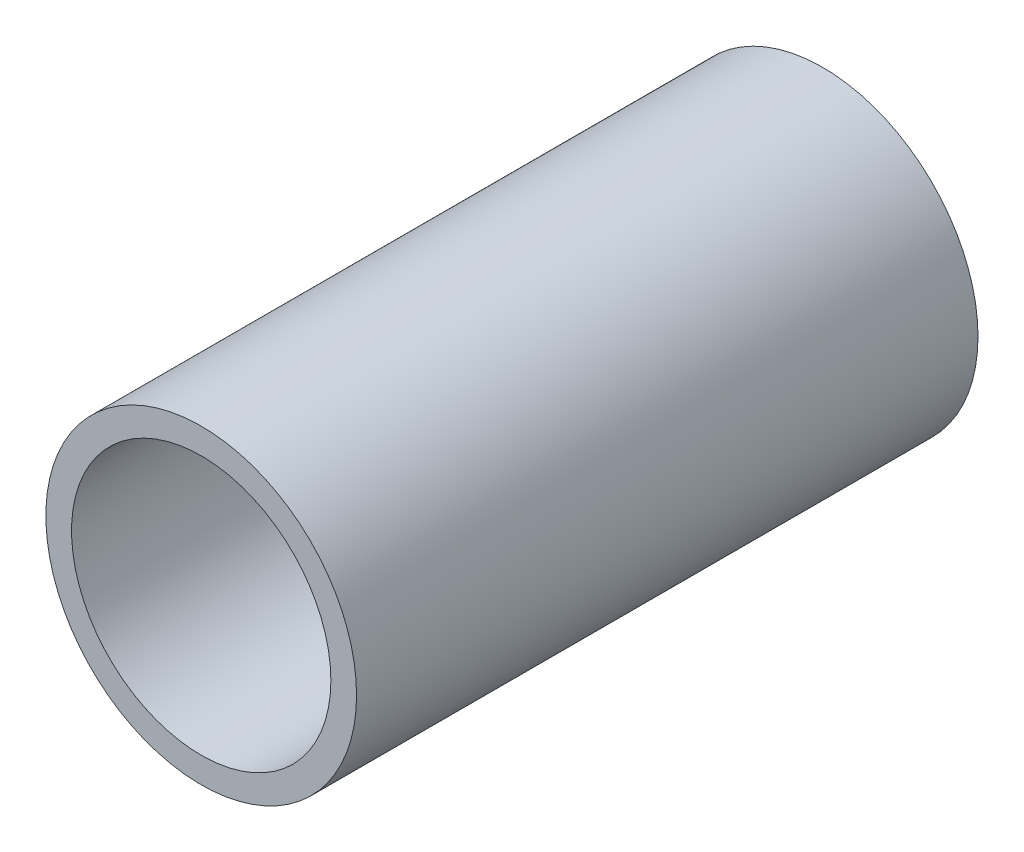
SolidWorks part; units mm, degrees
ref_plane "Front Plane" through (0, 0, 0) normal (0, 0, 1) x (1, 0, 0)
ref_plane "Top Plane" through (0, 0, 0) normal (0, 1, 0) x (1, 0, 0)
ref_plane "Right Plane" through (0, 0, 0) normal (1, 0, 0) x (0, 0, -1)
sketch "Sketch1" plane through (0, 0, 0) normal (0, 0, 1) x (1, 0, 0)
  circle A0 centre (0, 0) radius 15.9
  circle A1 centre (0, 0) radius 19.05
  dimension "D1" = 38.1
  dimension "D2" = 31.8
extrude "Boss-Extrude1" add sketch "Sketch1" along normal blind 76.2
